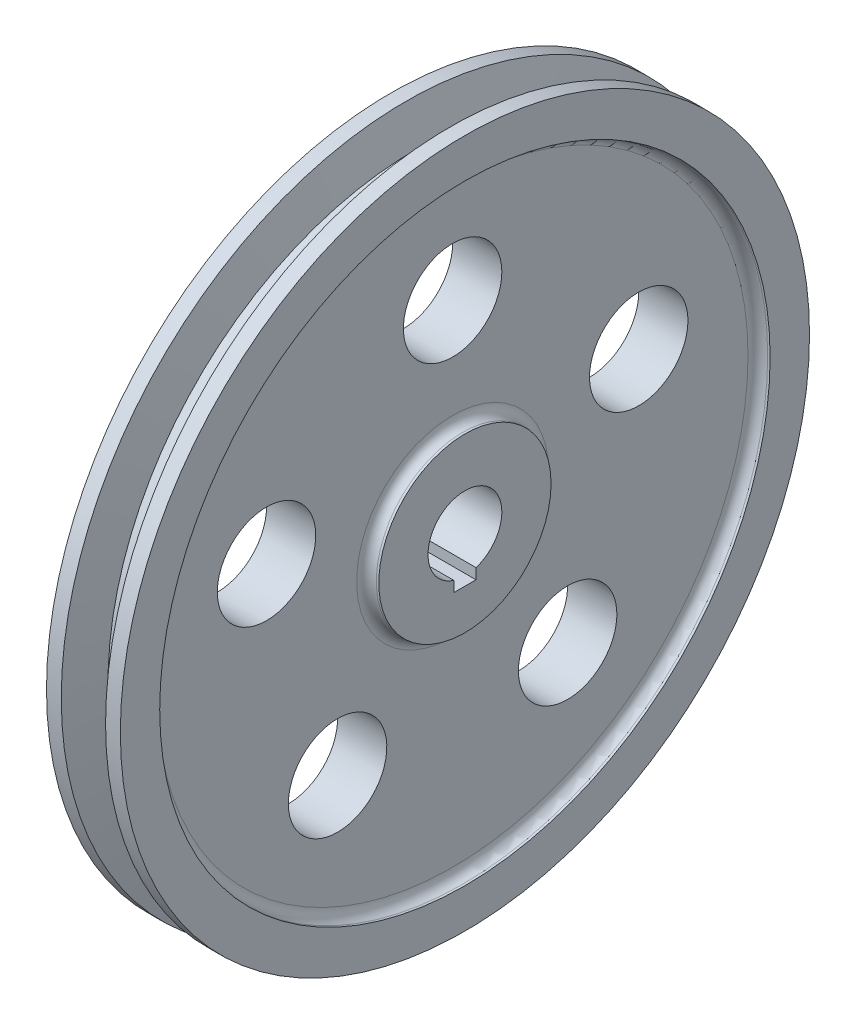
SolidWorks part; units mm, degrees
ref_plane "Front Plane" through (0, 0, 0) normal (0, 0, 1) x (1, 0, 0)
ref_plane "Top Plane" through (0, 0, 0) normal (0, 1, 0) x (1, 0, 0)
ref_plane "Right Plane" through (0, 0, 0) normal (1, 0, 0) x (0, 0, -1)
sketch "Sketch1" plane through (0, 0, 0) normal (0, 0, 1) x (1, 0, 0)
  line L0 (-7.5, 7.5) -> (7.5, 7.5)
  line L1 (-7.5, 7.5) -> (-7.5, 17.5)
  line L2 (0, 0) -> (0, 97.5393) construction
  line L3 (-7.5, 17.5) -> (-7, 17.5)
  line L4 (-5, 19.5) -> (-5, 60)
  line L5 (-7, 62) -> (-7.5, 62)
  line L6 (-7.5, 62) -> (-7.5, 70)
  line L7 (-7.5, 70) -> (-4.5, 70)
  line L8 (-4.5, 70) -> (-2.5, 62.5)
  line L9 (-2.5, 62.5) -> (2.5, 62.5)
  line L10 (4.5, 70) -> (2.5, 62.5)
  line L11 (7.5, 70) -> (4.5, 70)
  line L12 (7.5, 62) -> (7.5, 70)
  line L13 (7, 62) -> (7.5, 62)
  line L14 (5, 19.5) -> (5, 60)
  line L15 (7.5, 17.5) -> (7, 17.5)
  line L16 (7.5, 7.5) -> (7.5, 17.5)
  arc A0 (-5, 60) -> (-7, 62) centre (-7, 60) ccw
  arc A1 (-7, 17.5) -> (-5, 19.5) centre (-7, 19.5) ccw
  arc A2 (5, 60) -> (7, 62) centre (7, 60) cw
  arc A3 (7, 17.5) -> (5, 19.5) centre (7, 19.5) cw
  point P18 (0, 62.5)
  point P29 (0, 7.5)
  dimension "D1" = 2
  dimension "D2" = 7.5
  dimension "D3" = 7.5
  dimension "D4" = 5
  dimension "D5" = 62.5
  dimension "D6" = 62.5
  dimension "D7" = 10
  dimension "D8" = 8
  dimension "D10" = 2.5
  dimension "D11" = 7.5
ref_axis "Axis1" through (25.864, 0, 0) along (-1, 0, 0)
revolve "Revolve1" add sketch "Sketch1" angle 360 about axis through (25.864, 0, 0) along (-1, 0, 0)
sketch "Sketch2" plane through (5, 0, 0) normal (1, 0, 0) x (0, 0, -1)
  line L0 (0, 60) -> (0, 19.5) construction
  circle A0 centre (0, 0) radius 60 construction
  circle A1 centre (0, 0) radius 19.5 construction
  circle A2 centre (0, 39.75) radius 10
  point P2 (0, 39.75)
  dimension "D1" = 20
extrude "Extrude1" cut sketch "Sketch2" against normal blind 10
pattern_circular "CirPattern1" count 5 over 360 about axis through (0, 0, 0) along (1, 0, 0) of "Extrude1"
sketch "Sketch3" plane through (7.5, 0, 0) normal (1, 0, 0) x (0, 0, -1)
  line L1 (-2.25, -7) -> (2.25, -7)
  line L2 (-2.25, -7) -> (-2.25, -9.3)
  line L3 (-2.25, -9.3) -> (2.25, -9.3)
  line L4 (2.25, -7) -> (2.25, -9.3)
  point P4 (0, -7)
  dimension "D1" = 2.3
  dimension "D2" = 4.5
  dimension "D3" = 7
extrude "Extrude2" cut sketch "Sketch3" against normal through all
